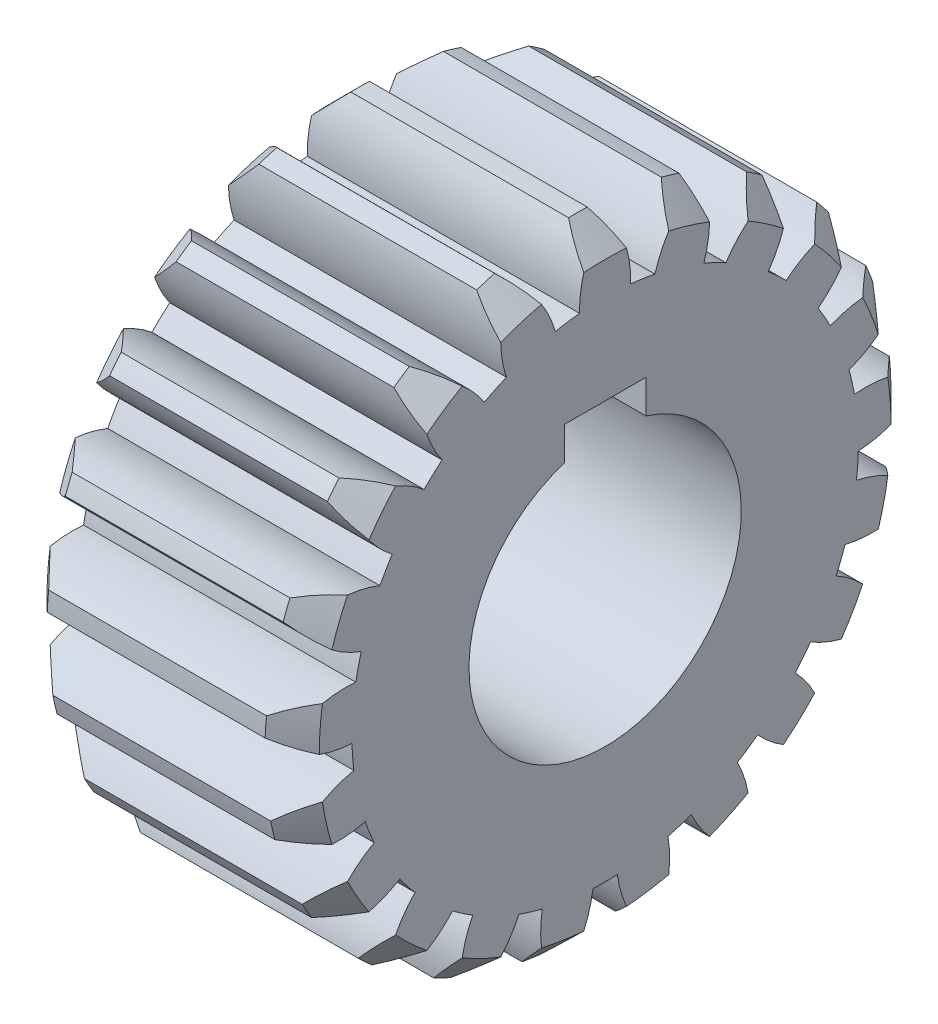
SolidWorks part; units mm, degrees
material "Сталь ШХ15 ГОСТ 801-78"
ref_plane "Plane1" through (0, 0, 0) normal (0, 0, 1) x (1, 0, 0)
ref_plane "Plane2" through (0, 0, 0) normal (0, 1, 0) x (1, 0, 0)
ref_plane "Plane3" through (0, 0, 0) normal (1, 0, 0) x (0, 0, -1)
sketch "Эскиз1" plane through (0, 0, 0) normal (0, 0, 1) x (1, 0, 0)
  line L0 (0, 0) -> (-28.3543, 0) construction
  line L1 (-10, 10) -> (10, 10)
  line L2 (10, 10) -> (10, 23)
  line L3 (10, 23) -> (-10, 23)
  line L4 (-10, 23) -> (-10, 10)
  line L5 (0, 10) -> (0, 0) construction
  dimension "D1" = 20
  dimension "D2" = 46
  dimension "D3" = 20
revolve "Повернуть1" add sketch "Эскиз1" angle 360 about L0
chamfer "Фаска1" distance 2 angle 45 2 edges at (10, 0, -23) (-10, 0, -23)
sketch "Sketch3" plane through (10, 9.4978, -4.3364) normal (1, 0, 0) x (0, 0, -1)
  line L0 (-4.3364, -9.4978) -> (-0.9085, 13.2453) construction
  line L1 (-4.3364, -9.4978) -> (16.6636, -9.4978) construction
  line L2 (16.6636, -9.4978) -> (18.6636, -9.4978) construction
  line L3 (-2.7671, 11.4435) -> (-4.3364, -9.4978) construction
  line L4 (-4.3364, -9.4978) -> (-4.3364, 6.5022) construction
  line L5 (-2.7671, 11.4435) -> (-1.1098, 11.9098) construction
  line L6 (18.6636, -9.4978) -> (19.6636, -9.4978) construction
  line L7 (19.6636, -9.4978) -> (18.6636, -7.4978) construction
  line L8 (19.6636, -7.4978) -> (19.6636, -9.4978) construction
  circle A0 centre (-4.3364, -9.4978) radius 21 construction
  circle A1 centre (-4.3364, -9.4978) radius 21 construction
  circle A2 centre (-4.3364, -9.4978) radius 18.6 construction
  arc A3 (-2.4547, 9.0067) -> (-3.6513, 13.492) centre (-10.8532, 9.1684) ccw
  arc A5 (1.7852, 12.6725) -> (-3.6513, 13.492) centre (-4.3364, -9.4978) ccw
  arc A6 (-0.6803, 8.7393) -> (-2.4547, 9.0067) centre (-4.3364, -9.4978) ccw
  arc A7 (1.7852, 12.6725) -> (-0.6803, 8.7393) centre (7.3927, 6.4183) ccw
  dimension "D6" = 8.4
  dimension "D3" = 8.571
  dimension "D4" = 4.286
  dimension "D5" = 70
  dimension "D7" = 81.429
  dimension "Смещение_плюс_один" = 1
  dimension "Коэфф_уравнительного_смещения_плюс_один" = 1
extrude "Cut-Extrude1-Впадина зуба" cut sketch "Sketch3" against normal blind 50
pattern_circular "CirPattern2" count 21 over 360 about axis through (0, 0, 0) along (1, 0, 0) of "Cut-Extrude1-Впадина зуба"
other "Зубчатый венец<1>"
sketch "Эскиз2" plane through (0, 0, 0) normal (1, 0, 0) x (0, 0, -1)
  line L1 (-3, 0) -> (3, 0)
  line L2 (-3, 0) -> (-3, 12)
  line L3 (-3, 12) -> (3, 12)
  line L4 (3, 0) -> (3, 12)
  dimension "D1" = 6
  dimension "D2" = 12
extrude "Вырез-Вытянуть1" cut sketch "Эскиз2" against normal through all both and the other way through all
equation "\"Средний@Sketch3\" = \"Делительный@Sketch3\" + 2 * \"D0_модуль@Sketch3\" *  ( \"Смещение_плюс_один@Sketch3\" - 1 ) "
equation "\"D1@CirPattern2\" = \"D0_число_зубьев@Sketch3\""
equation "\"Диаметр_вершин@Sketch3\" = \"Средний@Sketch3\" + 2 * ( \"D0_модуль@Sketch3\" - ( \"Коэфф_уравнительного_смещения_плюс_один@Sketch3\" - 1 ) )"
equation "\"Диаметр_впадин@Sketch3\" = \"Средний@Sketch3\" - 2.4 * \"D0_модуль@Sketch3\""
equation "\"D3@Sketch3\" = 180 / \"D0_число_зубьев@Sketch3\""
equation "\"D4@Sketch3\" = 90 / \"D0_число_зубьев@Sketch3\""
equation "\"Делительный@Sketch3\"= \"D0_число_зубьев@Sketch3\" * \"D0_модуль@Sketch3\""
equation "\"D6@Sketch3\" = \"D0_число_зубьев@Sketch3\" * \"D0_модуль@Sketch3\" / 5"
